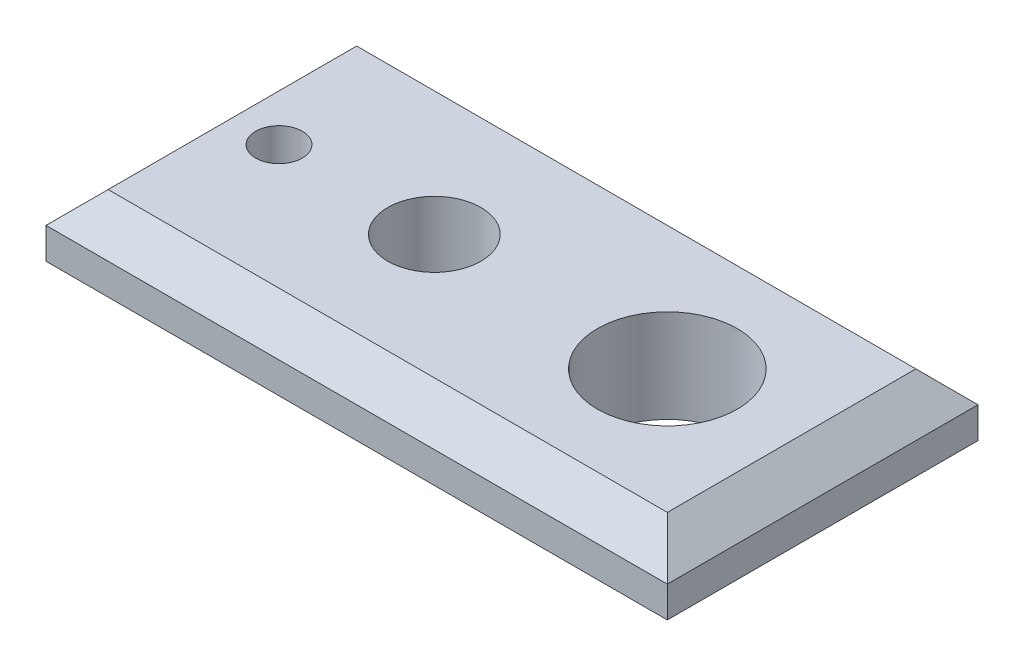
SolidWorks part; units mm, degrees
ref_plane "Ön Düzlem" through (0, 0, 0) normal (0, 0, 1) x (1, 0, 0)
ref_plane "Üst Düzlem" through (0, 0, 0) normal (0, 1, 0) x (1, 0, 0)
ref_plane "Sağ Düzlem" through (0, 0, 0) normal (1, 0, 0) x (0, 0, -1)
sketch "Çizim1" plane through (0, 0, 0) normal (0, 1, 0) x (1, 0, 0)
  line L5 (0, 0) -> (-200, 0)
  line L6 (0, 0) -> (0, 100)
  line L7 (0, 100) -> (-200, 100)
  line L8 (-200, 0) -> (-200, 100)
  dimension "D1" = 200
  dimension "D2" = 100
extrude "Yükseklik-Ekstrüzyon1" add sketch "Çizim1" along normal blind 30
chamfer "Pah1" distance 10 angle 45 8 edges at (-100, 0, -100) (-200, 0, -50) (-100, 0, 0) (0, 0, -50) (-100, 30, 0) (-200, 30, -50) (-100, 30, -100) (0, 30, -50)
sketch "Çizim2" plane through (0, 30, 0) normal (0, 1, 0) x (1, 0, 0)
  line L0 (-200, 50) -> (0, 50) construction
  line L1 (-200, 0) -> (-200, 100) construction
  line L2 (0, 100) -> (0, 0) construction
  circle A0 centre (-175, 50) radius 7.5
  circle A1 centre (-125, 50) radius 15
  circle A2 centre (-50, 50) radius 22.5
  dimension "D1" = 15
  dimension "D2" = 30
  dimension "D3" = 45
  dimension "D4" = 25
  dimension "D5" = 50
  dimension "D6" = 75
extrude "Kes-Ekstrüzyon1" cut sketch "Çizim2" against normal through all
